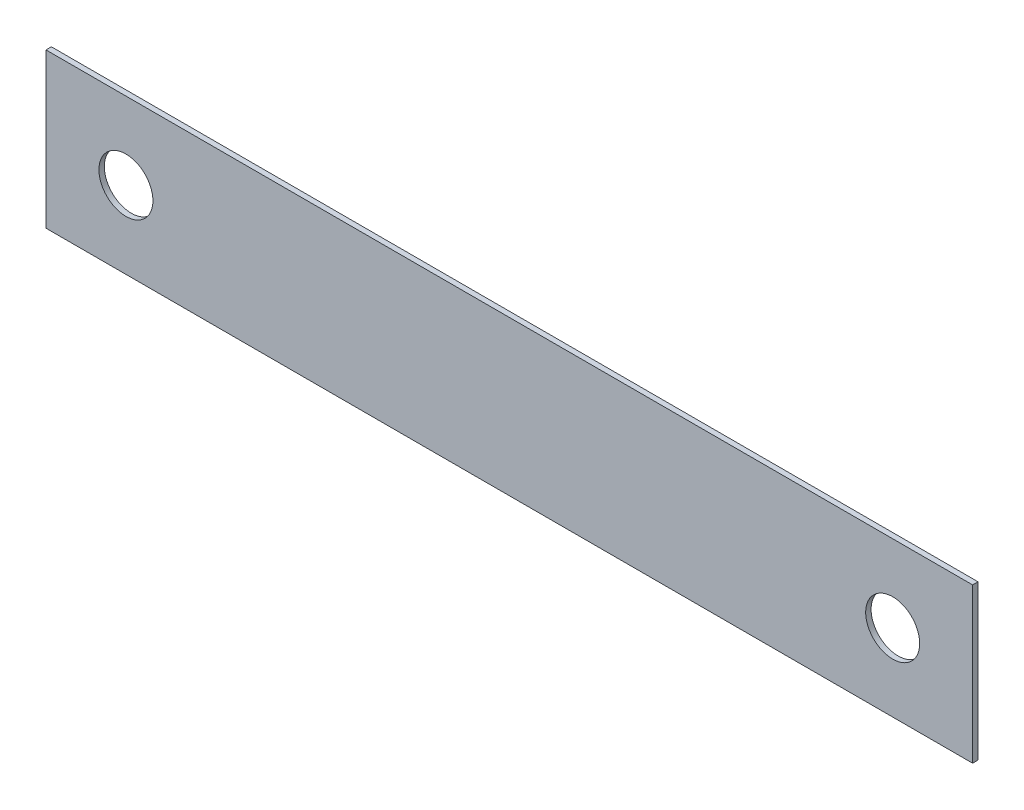
SolidWorks part; units mm, degrees
material "Chrome Stainless Steel"
ref_plane "Front Plane" through (0, 0, 0) normal (0, 0, 1) x (1, 0, 0)
ref_plane "Top Plane" through (0, 0, 0) normal (0, 1, 0) x (1, 0, 0)
ref_plane "Right Plane" through (0, 0, 0) normal (1, 0, 0) x (0, 0, -1)
sketch "Sketch1" plane through (0, 0, 0) normal (0, 0, 1) x (1, 0, 0)
  line L0 (-15.248, 7.15) -> (106.9472, 7.15) construction
  line L1 (0, 0) -> (85.8, 0)
  line L2 (0, 0) -> (0, 14.3)
  line L3 (0, 14.3) -> (85.8, 14.3)
  line L4 (85.8, 0) -> (85.8, 14.3)
  line L5 (42.9, 17.8893) -> (42.9, -4.569) construction
  circle A0 centre (7.4, 7.15) radius 2.5
  circle A1 centre (78.4, 7.15) radius 2.5
  dimension "D3" = 5
  dimension "D4" = 5
  dimension "D1" = 85.8
  dimension "D2" = 14.3
  dimension "D5" = 71
extrude "Boss-Extrude1" add sketch "Sketch1" along normal blind 0.5
